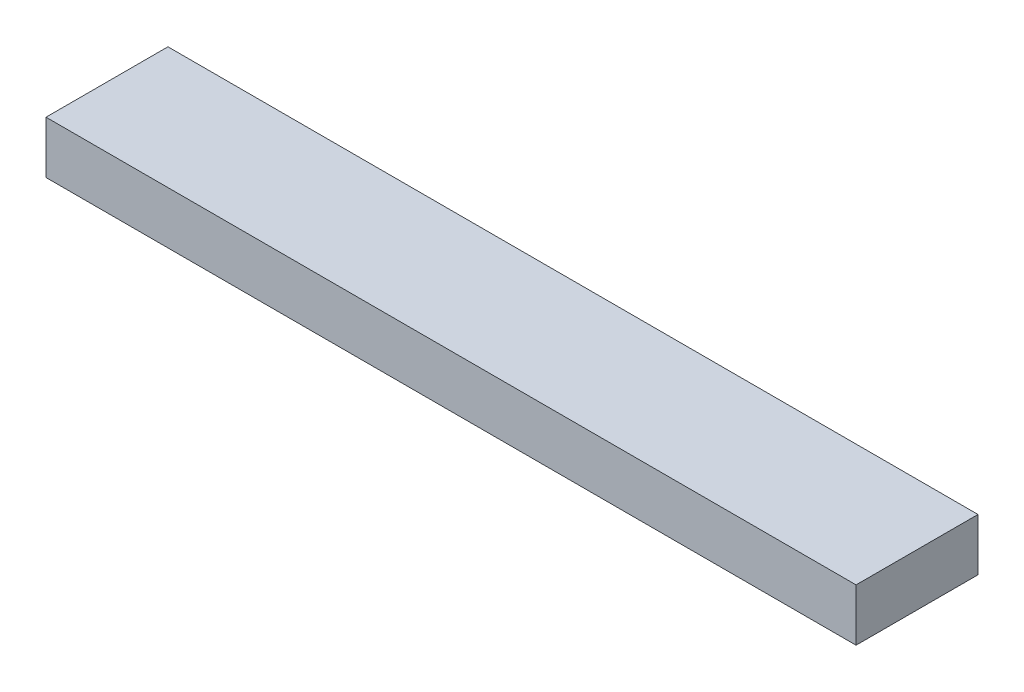
SolidWorks part; units mm, degrees
ref_plane "Front Plane" through (0, 0, 0) normal (0, 0, 1) x (1, 0, 0)
ref_plane "Top Plane" through (0, 0, 0) normal (0, 1, 0) x (1, 0, 0)
ref_plane "Right Plane" through (0, 0, 0) normal (1, 0, 0) x (0, 0, -1)
sketch "Sketch1" plane through (0, 0, 0) normal (0, 1, 0) x (1, 0, 0)
  line L1 (0, 0) -> (590.55, 0)
  line L2 (0, 0) -> (0, 88.9)
  line L3 (0, 88.9) -> (590.55, 88.9)
  line L4 (590.55, 0) -> (590.55, 88.9)
  dimension "D1" = 88.9
  dimension "D2" = 590.55
extrude "Boss-Extrude1" add sketch "Sketch1" along normal blind 38.1
